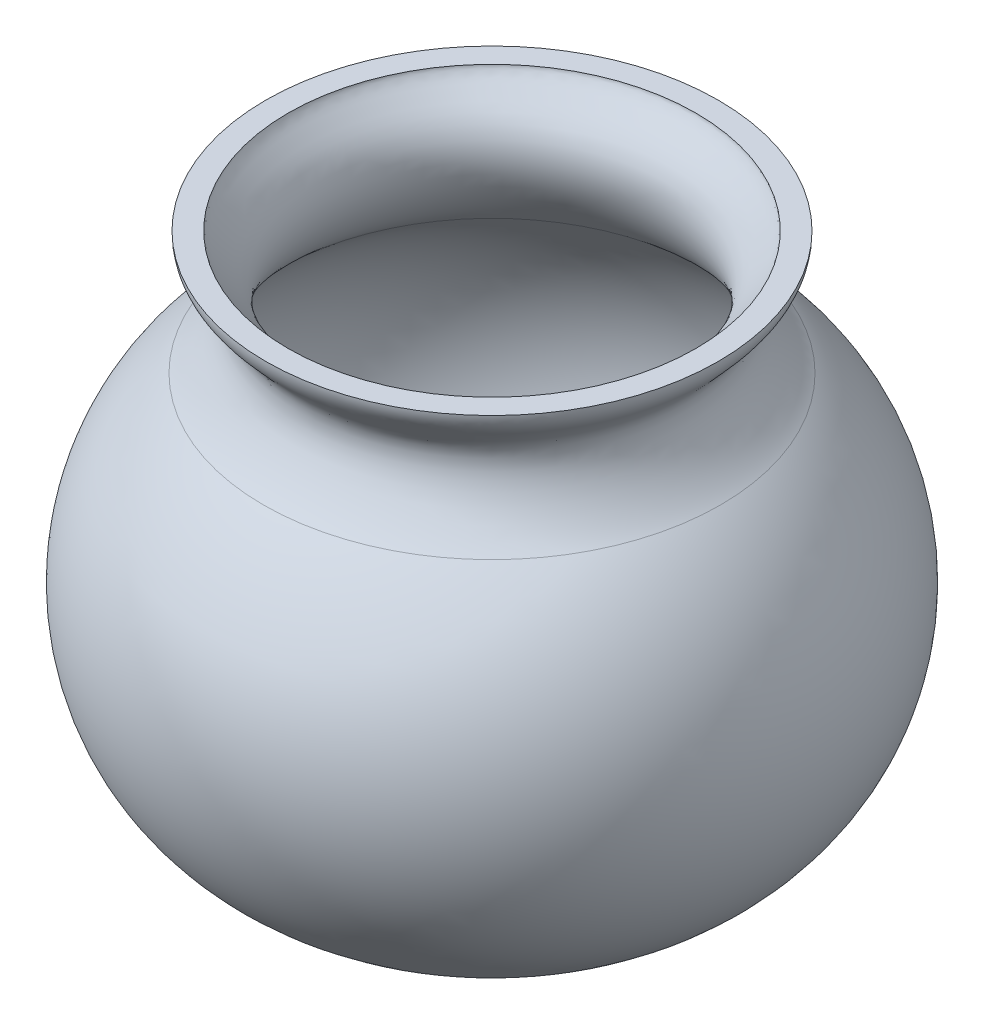
SolidWorks part; units mm, degrees
material "Maple"
ref_plane "Front Plane" through (0, 0, 0) normal (0, 0, 1) x (1, 0, 0)
ref_plane "Top Plane" through (0, 0, 0) normal (0, 1, 0) x (1, 0, 0)
ref_plane "Right Plane" through (0, 0, 0) normal (1, 0, 0) x (0, 0, -1)
sketch "Sketch1" plane through (0, 0, 0) normal (0, 0, 1) x (1, 0, 0)
  line L0 (0, 58.5221) -> (0, -32.8161) construction
  line L1 (0, -23.6953) -> (6.4968, -23.6953)
  line L2 (0, -21.9453) -> (6.4968, -21.9453)
  line L3 (0, -21.9453) -> (0, -23.6953)
  line L4 (15.926, 18.1853) -> (17.676, 18.1853)
  arc A0 (6.4968, -23.6953) -> (17.8417, 8.5535) centre (6.4968, -5.5754) ccw
  arc A1 (6.4968, -21.9453) -> (16.7461, 7.1889) centre (6.4968, -5.5754) ccw
  arc A2 (6.4968, -23.6953) -> (17.8417, 8.5535) centre (6.4968, -5.5754) ccw construction
  spline S0 degree 3 poles (17.8417, 8.5535) (16.3632, 9.7406) (13.0542, 14.3831) (17.676, 16.5435) (17.676, 18.1853) knots 0 0 0 0 0.57429 1 1 1 1
  spline S1 degree 1 poles (16.7461, 7.1889) (15.926, 18.1853) knots 0 0 1 1 construction
  spline S2 degree 3 poles (16.7461, 7.1889) (16.533, 7.36) (16.1324, 7.7159) (15.3296, 8.5556) (14.3961, 9.7886) (13.6628, 11.2286) (13.3167, 12.5197) (13.2326, 13.564) (13.4151, 14.6956) (13.9429, 15.7271) (14.5266, 16.4439) (15.0771, 17.0246) (15.5281, 17.5012) (15.8201, 17.8789) (15.9221, 18.105) (15.926, 18.149) (15.926, 18.1853) knots 0 0 0 0 0.0625 0.125 0.25 0.375 0.4375 0.5 0.5625 0.625 0.6875 0.75 0.8125 0.875 0.9375 1 1 1 1
  point P0 (6.4968, -23.6953)
  point P5 (15.9572, 18.689)
  point P11 (15.1468, 14.2832)
  point P12 (17.6915, 18.9783)
  point P13 (0, 0)
  dimension "D1" = 1.75
revolve "Revolve2" add sketch "Sketch1" angle 360 about L0
sketch "Sketch2" plane through (0, -23.6953, 0) normal (0, -1, 0) x (1, 0, 0)
  line L0 (0, 3.9008) -> (0, -4.551) construction
  line L1 (3.5502, 0) -> (-3.7057, 0) construction
  circle A0 centre (2.25, 2.25) radius 1.25
  circle A1 centre (-2.25, 2.25) radius 1.25
  circle A2 centre (2.25, -2.25) radius 1.25
  circle A3 centre (-2.25, -2.25) radius 1.25
  dimension "D1" = 2.25
  dimension "D3" = 2.5
  dimension "D2" = 2.25
extrude "Cut-Extrude1" cut sketch "Sketch2" against normal up to next
